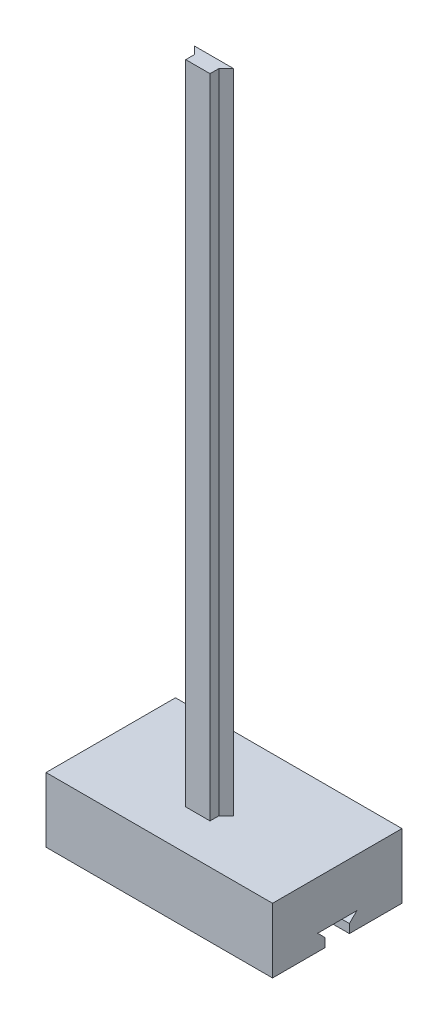
SolidWorks part; units mm, degrees
ref_plane "Front Plane" through (0, 0, 0) normal (0, 0, 1) x (1, 0, 0)
ref_plane "Top Plane" through (0, 0, 0) normal (0, 1, 0) x (1, 0, 0)
ref_plane "Right Plane" through (0, 0, 0) normal (1, 0, 0) x (0, 0, -1)
sketch "Sketch1" plane through (0, 0, 0) normal (0, 1, 0) x (1, 0, 0)
  line L1 (0, 0) -> (177.8, 0)
  line L2 (0, 0) -> (0, 101.6)
  line L3 (0, 101.6) -> (177.8, 101.6)
  line L4 (177.8, 0) -> (177.8, 101.6)
  dimension "D1" = 177.8
  dimension "D2" = 101.6
extrude "Boss-Extrude1" add sketch "Sketch1" along normal blind 50.8
sketch "Sketch2" plane through (177.8, 0, 0) normal (1, 0, 0) x (0, 0, -1)
  line L0 (41.275, 0) -> (41.275, 6.858)
  line L1 (0, 0) -> (101.6, 0) construction
  line L2 (41.275, 6.858) -> (35.433, 12.7)
  line L3 (35.433, 12.7) -> (66.167, 12.7)
  line L4 (66.167, 12.7) -> (60.325, 6.858)
  line L5 (60.325, 6.858) -> (60.325, 0)
  line L6 (60.325, 0) -> (41.275, 0)
  line L7 (0, 50.8) -> (0, 0) construction
  dimension "D1" = 12.7
  dimension "D2" = 19.05
  dimension "D3" = 45
  dimension "D4" = 45
  dimension "D5" = 30.734
  dimension "D6" = 6.858
  dimension "D7" = 41.275
extrude "Cut-Extrude1" cut sketch "Sketch2" against normal through all
sketch "Sketch3" plane through (0, 50.8, 0) normal (0, 1, 0) x (1, 0, 0)
  line L0 (78.2426, 31.4297) -> (78.2426, 38.2877)
  line L1 (78.2426, 38.2877) -> (72.4006, 44.1297)
  line L2 (72.4006, 44.1297) -> (103.1346, 44.1297)
  line L3 (103.1346, 44.1297) -> (97.2926, 38.2877)
  line L4 (97.2926, 38.2877) -> (97.2926, 31.4297)
  line L5 (97.2926, 31.4297) -> (78.2426, 31.4297)
extrude "Boss-Extrude2" add sketch "Sketch3" along normal blind 508
